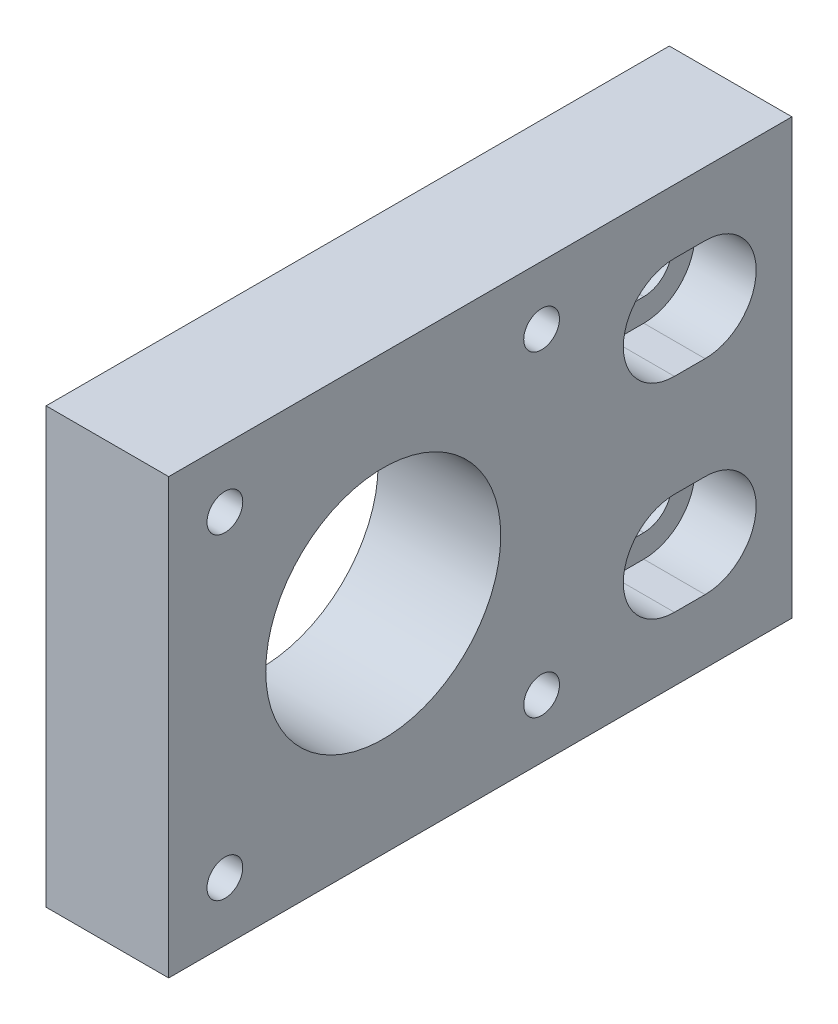
SolidWorks part; units mm, degrees
ref_plane "Front Plane" through (0, 0, 0) normal (0, 0, 1) x (1, 0, 0)
ref_plane "Top Plane" through (0, 0, 0) normal (0, 1, 0) x (1, 0, 0)
ref_plane "Right Plane" through (0, 0, 0) normal (1, 0, 0) x (0, 0, -1)
sketch "Sketch2" plane through (0, 0, 0) normal (1, 0, 0) x (0, 0, -1)
  line L0 (0, 0) -> (-21, 0) construction
  line L1 (-21, 0) -> (-21, -21.25) construction
  line L3 (-21, -21.25) -> (40, -21.25)
  line L4 (-21, -21.25) -> (-21, 21.25)
  line L5 (-21, 21.25) -> (40, 21.25)
  line L6 (40, -21.25) -> (40, 21.25)
  line L7 (30, 21.25) -> (30, -21.25) construction
  line L8 (28.5, 10) -> (31.5, 10) construction
  line L9 (28.5, 12.75) -> (31.5, 12.75)
  line L10 (28.5, 7.25) -> (31.5, 7.25)
  line L11 (28.5, -10) -> (31.5, -10) construction
  line L12 (28.5, -12.75) -> (31.5, -12.75)
  line L13 (28.5, -7.25) -> (31.5, -7.25)
  circle A0 centre (0, 0) radius 11.5
  circle A1 centre (-15.5, 15.5) radius 1.75
  circle A2 centre (15.5, -15.5) radius 1.75
  circle A3 centre (15.5, 15.5) radius 1.75
  circle A4 centre (-15.5, -15.5) radius 1.75
  arc A5 (28.5, 12.75) -> (28.5, 7.25) centre (28.5, 10) ccw
  arc A6 (31.5, 7.25) -> (31.5, 12.75) centre (31.5, 10) ccw
  arc A7 (28.5, -12.75) -> (28.5, -7.25) centre (28.5, -10) cw
  arc A8 (31.5, -7.25) -> (31.5, -12.75) centre (31.5, -10) cw
  point P21 (30, 10)
  point P28 (30, -10)
  dimension "D1" = 23
  dimension "D7" = 15.5
  dimension "D8" = 3.5
  dimension "D9" = 3.5
  dimension "D10" = 15.5
  dimension "D13" = 5.5
  dimension "D15" = 15.5
  dimension "D6" = 15.5
  dimension "D2" = 21
  dimension "D3" = 21.25
  dimension "D4" = 42.5
  dimension "D5" = 61
  dimension "D11" = 10
  dimension "D12" = 10
  dimension "D14" = 3
extrude "Boss-Extrude2" add sketch "Sketch2" along normal blind 12
sketch "Sketch3" plane through (12, 0, 0) normal (1, 0, 0) x (0, 0, -1)
  line L0 (30, 12.75) -> (30, 7.25) construction
  line L1 (31.5, 12.75) -> (28.5, 12.75) construction
  line L2 (28.5, 7.25) -> (31.5, 7.25) construction
  line L3 (28.5, 10) -> (31.5, 10) construction
  line L4 (28.5, 15) -> (31.5, 15)
  line L5 (28.5, 5) -> (31.5, 5)
  line L6 (40, 0) -> (-21, 0) construction
  line L7 (40, -21.25) -> (40, 21.25) construction
  line L8 (-21, 21.25) -> (-21, -21.25) construction
  line L9 (28.5, -10) -> (31.5, -10) construction
  line L10 (28.5, -15) -> (31.5, -15)
  line L11 (28.5, -5) -> (31.5, -5)
  arc A0 (28.5, 15) -> (28.5, 5) centre (28.5, 10) ccw
  arc A1 (31.5, 5) -> (31.5, 15) centre (31.5, 10) ccw
  arc A3 (28.5, -15) -> (28.5, -5) centre (28.5, -10) cw
  arc A4 (31.5, -5) -> (31.5, -15) centre (31.5, -10) cw
  point P8 (30, 10)
  point P23 (30, -10)
  dimension "D1" = 10
extrude "Cut-Extrude1" cut sketch "Sketch3" against normal blind 6
